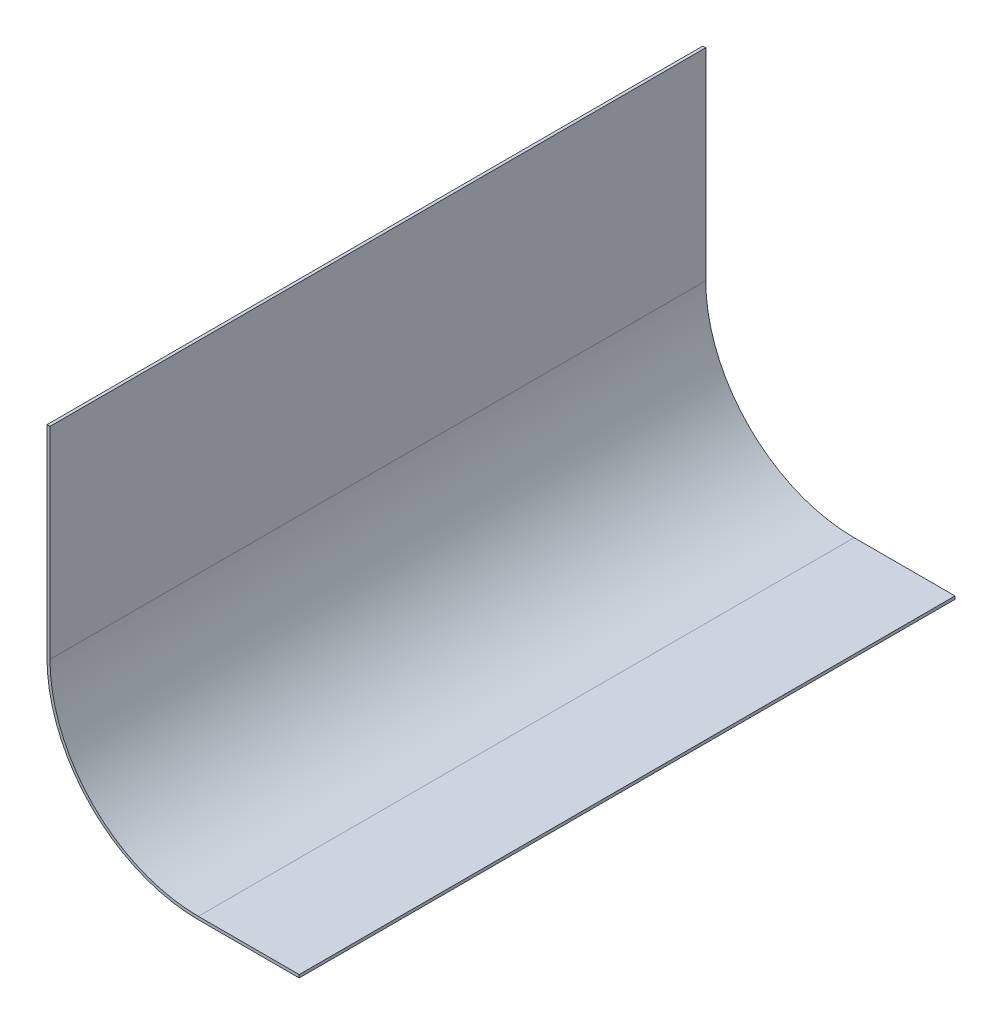
SolidWorks part; units mm, degrees
ref_plane "Front Plane" through (0, 0, 0) normal (0, 0, 1) x (1, 0, 0)
ref_plane "Top Plane" through (0, 0, 0) normal (0, 1, 0) x (1, 0, 0)
ref_plane "Right Plane" through (0, 0, 0) normal (1, 0, 0) x (0, 0, -1)
sketch "Sketch1" plane through (0, 0, 0) normal (0, 0, 1) x (1, 0, 0)
  line L0 (-418.175, 990.6) -> (-468.975, 990.6)
  line L1 (-418.175, 963.93) -> (-418.175, 990.6) construction
  line L2 (-545.175, 1066.8) -> (-545.175, 1168.4)
  arc A0 (-468.975, 990.6) -> (-545.175, 1066.8) centre (-468.975, 1066.8) cw
  dimension "D2" = 76.2
  dimension "D1" = 50.8
  dimension "D3" = 101.6
extrude "Extrude-Thin1" add sketch "Sketch1" along normal mid plane 330.2 thin
